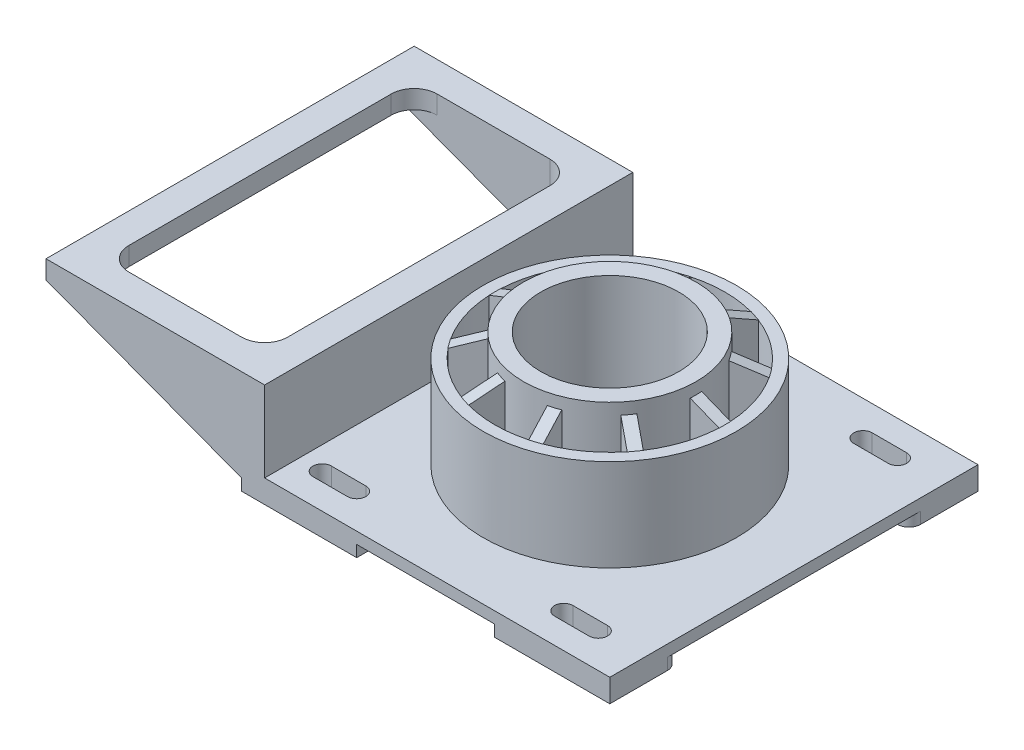
SolidWorks part; units mm, degrees
material "AISI 1020"
ref_plane "Front Plane" through (0, 0, 0) normal (0, 0, 1) x (1, 0, 0)
ref_plane "Top Plane" through (0, 0, 0) normal (0, 1, 0) x (1, 0, 0)
ref_plane "Right Plane" through (0, 0, 0) normal (1, 0, 0) x (0, 0, -1)
sketch "Sketch1" plane through (0, 0, 0) normal (0, 0, 1) x (1, 0, 0)
  line L0 (150, -40) -> (150, -35)
  line L1 (150, -35) -> (0, -35)
  line L2 (0, -35) -> (0, 0)
  line L3 (0, 0) -> (-95, 0)
  line L4 (-95, 0) -> (-95, -8)
  line L5 (-95, -8) -> (-10, -40)
  line L6 (-10, -40) -> (150, -40)
  dimension "D1" = 150
  dimension "D2" = 95
  dimension "D3" = 8
  dimension "D4" = 5
  dimension "D5" = 160
  dimension "D6" = 35
extrude "Boss-Extrude1" add sketch "Sketch1" along normal mid plane 160
sketch "Sketch2" plane through (0, 0, 0) normal (0, 1, 0) x (-1, 0, 0)
  line L0 (0, 80) -> (95, 80) construction
  line L1 (23, 67) -> (72, 67)
  line L2 (13, 57) -> (13, -57)
  line L3 (23, -67) -> (72, -67)
  line L4 (82, 57) -> (82, -57)
  line L5 (95, 80) -> (95, -80) construction
  line L6 (0, -80) -> (95, -80) construction
  line L7 (0, 80) -> (0, -80) construction
  arc A0 (23, 67) -> (13, 57) centre (23, 57) ccw
  arc A1 (13, -57) -> (23, -67) centre (23, -57) ccw
  arc A2 (72, -67) -> (82, -57) centre (72, -57) ccw
  arc A3 (72, 67) -> (82, 57) centre (72, 57) cw
  dimension "D1" = 10
  dimension "D2" = 13
  dimension "D3" = 13
  dimension "D4" = 13
  dimension "D5" = 13
extrude "Cut-Extrude1" cut sketch "Sketch2" against normal up to next
sketch "Sketch3" plane through (-95, 0, 0) normal (-1, 0, 0) x (0, 0, 1)
  line L0 (-67, -35.1059) -> (-67, 0) construction
  line L1 (67, -16.6588) -> (-67, -16.6588)
  line L2 (67, -16.6588) -> (67, -8)
  line L3 (67, -8) -> (-67, -8)
  line L4 (-67, -16.6588) -> (-67, -8)
  line L5 (80, -8) -> (-80, -8) construction
  line L6 (67, -35.1059) -> (67, -16.6588) construction
  ellipse E0 centre (57, -16.6588) end of major axis (47, -16.6588) minor radius 3.7647 (67, -16.6588) -> (57, -12.8941) ccw construction
extrude "Cut-Extrude2" cut sketch "Sketch3" against normal up to next
sketch "Sketch4" plane through (0, -40, 0) normal (0, -1, 0) x (-1, 0, 0)
  line L0 (-70, 232.5) -> (-70, -80) construction
  line L2 (10, -80) -> (-150, -80) construction
  circle A0 centre (-70, 0) radius 25
  circle A1 centre (-70, 0) radius 20
  point P6 (-70, 76.25)
  dimension "D1" = 50
  dimension "D2" = 40
extrude "Boss-Extrude2" add sketch "Sketch4" along normal blind 30
sketch "Sketch5" plane through (0, -40, 0) normal (0, -1, 0) x (-1, 0, 0)
  line L59 (10, -80) -> (10, 80) construction
  line L60 (-150, 80) -> (-100, 80)
  line L61 (-150, 80) -> (-150, 50)
  line L62 (-150, 50) -> (-100, 50)
  line L63 (-100, 80) -> (-100, 50)
  line L64 (10, 80) -> (-40, 80)
  line L65 (10, 80) -> (10, 50)
  line L66 (10, 50) -> (-40, 50)
  line L67 (-40, 80) -> (-40, 50)
  line L68 (10, 80) -> (-150, 80) construction
  line L70 (10, -80) -> (-40, -80)
  line L71 (10, -80) -> (10, -50)
  line L72 (10, -50) -> (-40, -50)
  line L73 (-40, -80) -> (-40, -50)
  line L74 (-150, -80) -> (-100, -80)
  line L75 (-150, -80) -> (-150, -50)
  line L76 (-150, -50) -> (-100, -50)
  line L77 (-100, -80) -> (-100, -50)
  dimension "D1" = 50
  dimension "D2" = 30
extrude "Boss-Extrude4" add sketch "Sketch5" along normal blind 5
fillet "Fillet1" radius 5 6 edges at (150, -42.5, 50) (100, -42.5, 50) (40, -42.5, 50) (40, -42.5, -50) (150, -42.5, -50) (100, -42.5, -50)
sketch "Sketch10" plane through (0, -45, 0) normal (0, -1, 0) x (-1, 0, 0)
  line L0 (-130, 65) -> (-115, 65) construction
  line L3 (-130, 69) -> (-115, 69)
  line L6 (-130, 61) -> (-115, 61)
  line L13 (-70, 56.2056) -> (-70, -56.2056) construction
  line L14 (-117.0572, 0) -> (-22.9428, 0) construction
  line L15 (-10, 65) -> (-25, 65) construction
  line L16 (-10, 69) -> (-25, 69)
  line L17 (-10, 61) -> (-25, 61)
  line L18 (-130, -65) -> (-115, -65) construction
  line L19 (-130, -69) -> (-115, -69)
  line L20 (-130, -61) -> (-115, -61)
  line L21 (-10, -65) -> (-25, -65) construction
  line L22 (-10, -69) -> (-25, -69)
  line L23 (-10, -61) -> (-25, -61)
  line L25 (-100, 55) -> (-100, 80) construction
  line L26 (-145, 50) -> (-105, 50) construction
  arc A8 (-130, 69) -> (-130, 61) centre (-130, 65) ccw
  arc A9 (-115, 61) -> (-115, 69) centre (-115, 65) ccw
  circle A10 centre (-70, 0) radius 20 construction
  arc A11 (-10, 69) -> (-10, 61) centre (-10, 65) cw
  arc A12 (-25, 61) -> (-25, 69) centre (-25, 65) cw
  arc A13 (-130, -69) -> (-130, -61) centre (-130, -65) cw
  arc A14 (-115, -61) -> (-115, -69) centre (-115, -65) cw
  arc A15 (-10, -69) -> (-10, -61) centre (-10, -65) ccw
  arc A16 (-25, -61) -> (-25, -69) centre (-25, -65) ccw
  point P2 (-122.5, 65)
  point P14 (-70, 0)
  point P17 (-70, 0)
  point P24 (-17.5, 65)
  point P33 (-122.5, -65)
  point P40 (-17.5, -65)
  dimension "D1" = 4
  dimension "D2" = 15
  dimension "D3" = 15
  dimension "D4" = 15
extrude "Cut-Extrude5" cut sketch "Sketch10" against normal up to next
sketch "Sketch11" plane through (0, -35, 0) normal (0, 1, 0) x (-1, 0, 0)
  circle A0 centre (-70, 0) radius 30
  circle A1 centre (-70, 0) radius 37.5
  circle A2 centre (-70, 0) radius 20 construction
  dimension "D1" = 60
  dimension "D2" = 75
extrude "Boss-Extrude6" add sketch "Sketch11" along normal blind 50
sketch "Sketch12" plane through (0, -35, 0) normal (0, 1, 0) x (-1, 0, 0)
  circle A0 centre (-70, 0) radius 50
  circle A1 centre (-70, 0) radius 55
  dimension "D1" = 100
  dimension "D2" = 110
extrude "Boss-Extrude7" add sketch "Sketch12" along normal blind 40
sketch "Sketch13" plane through (0, 0, 0) normal (0, 0, 1) x (1, 0, 0)
  line L1 (125, 5) -> (15, 5) construction
  line L2 (20, 5) -> (32.5, 10)
  line L4 (120, 5) -> (20, 5) construction
  line L6 (32.5, 15) -> (32.5, -35) construction
  dimension "D1" = 5
rib "Rib1" sketch "Sketch13" sketch "Sketch13" thickness 5 extrusion direction parallel to sketch draft on no parameters "D1"=5
pattern_circular "CirPattern1" count 10 over 360 about axis through (70, 0, 0) along (0, 1, 0) of "Rib1"
